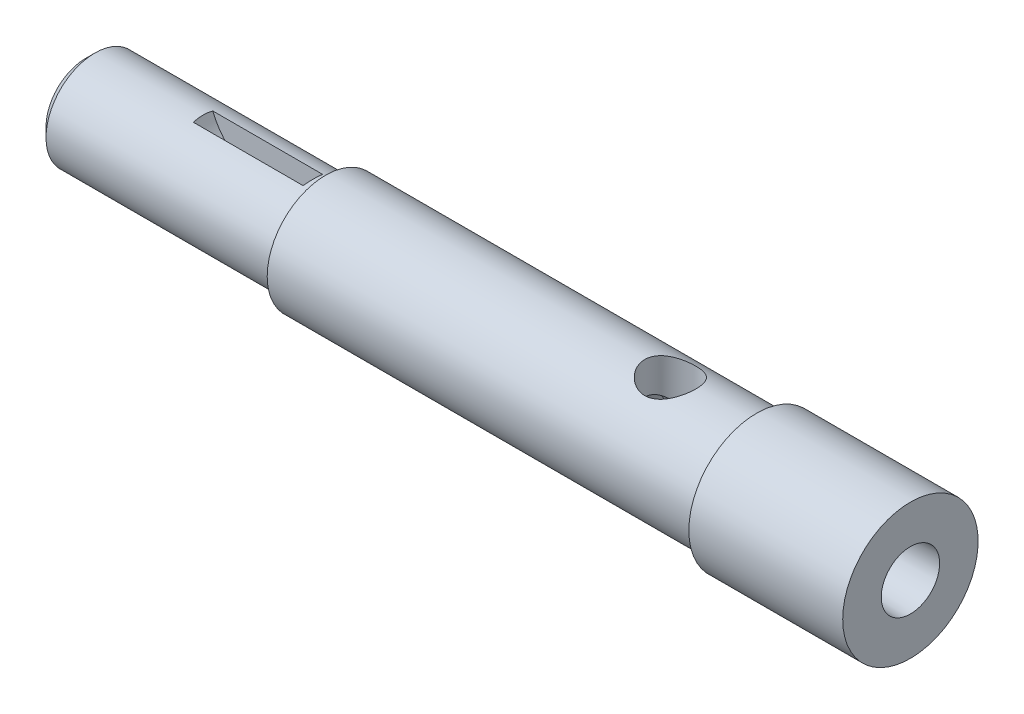
SolidWorks part; units mm, degrees
material "AISI 1020 Steel, Cold Rolled"
ref_plane "Front" through (0, 0, 0) normal (0, 0, 1) x (1, 0, 0)
ref_plane "Top" through (0, 0, 0) normal (0, 1, 0) x (1, 0, 0)
ref_plane "Right" through (0, 0, 0) normal (1, 0, 0) x (0, 0, -1)
sketch "Sketch1" plane through (0, 0, 0) normal (0, 0, 1) x (1, 0, 0)
  line L0 (-67, 0) -> (67, 0)
  line L1 (67, 0) -> (67, 11)
  line L2 (67, 11) -> (42, 11)
  line L3 (42, 11) -> (42, 9.5)
  line L4 (42, 9.5) -> (-28, 9.5)
  line L5 (-28, 9.5) -> (-28, 7.9375)
  line L6 (-28, 7.9375) -> (-67, 7.9375)
  line L7 (-67, 7.9375) -> (-67, 0)
  line L8 (-84.9355, 0) -> (103.2175, 0) construction
  dimension "D1" = 134
  dimension "D2" = 15.875
  dimension "D3" = 19
  dimension "D4" = 22
  dimension "D5" = 25
  dimension "D6" = 70
revolve "Revolve1" add sketch "Sketch1" angle 360 about L8
cosmetic thread "Cosmetic Thread1" parameters "D1"=15, "D2"=11.797
hole_wizard "1/8 NPT Tapped Hole1" positions "Sketch3" profile "Sketch2" size "1/8" standard "ANSI Inch"
sketch "Sketch3" plane through (67, 0, 0) normal (1, 0, 0) x (0, 0, -1)
  point P0 (0, 0)
sketch "Sketch2" plane through (67, 0, 0) normal (0, 1, 0) x (0, 0, -1)
  line L0 (0, 0) -> (0, 46.5335)
  line L1 (4.2164, 44) -> (0, 46.5335)
  line L2 (-4.2164, 44) -> (0, 46.5335) construction
  line L3 (4.2164, 44) -> (4.2164, 6.924)
  line L4 (4.2164, 6.924) -> (4.5374, 6.924)
  line L5 (4.5374, 6.924) -> (4.7447, 0)
  line L6 (-4.5374, 6.924) -> (-4.7447, 0) construction
  line L7 (4.7447, 0) -> (0, 0)
  line L8 (0, -6.35) -> (0, 107.95) construction
  line L11 (-4.2164, 6.924) -> (-4.5374, 6.924) construction
  dimension "Tap Drill Dia." = 8.4328
  dimension "Tap Drill Depth" = 44
  dimension "Thread Dia." = 9.4894
  dimension "Thread Angle" = 3.43
  dimension "Thread Depth" = 6.924
  dimension "Drill Angle" = 118
cosmetic thread "Hole Thread1" parameters "D1"=6.924, "D2"=10.287
sketch "Sketch4" plane through (0, 0, 0) normal (0, 1, 0) x (1, 0, 0)
  line L0 (42, 11) -> (42, -11) construction
  circle A0 centre (28, 0) radius 4.15
  dimension "D1" = 8.3
  dimension "D2" = 14
extrude "Cut-Extrude1" cut sketch "Sketch4" against normal mid plane 30
chamfer "Chamfer1" distance 1.5 angle 45 1 edges at (-67, 0, 7.9375)
ref_plane "Plane1" [suppressed] through (0, 12.6375, 0) normal (0, 1, 0) x (-1, 0, 0)
sketch "Sketch7" plane through (0, 0, 0) normal (0, 0, 1) x (1, 0, 0)
  line L0 (-28, 7.9375) -> (-65.5, 7.9375) construction
  line L1 (-55.271, 11.1125) -> (-19.7707, 11.1125) construction
  line L2 (-39, 28.0953) -> (-39, -15.815) construction
  line L3 (-28, 9.5) -> (-28, -9.5) construction
  line L4 (-48.3918, 9.525) -> (-29.6082, 9.525)
  arc A0 (-48.3918, 9.525) -> (-29.6082, 9.525) centre (-39, 11.1125) ccw
  point P5 (-39, 1.5875)
  dimension "D3" = 9.525
  dimension "D2" = 3.175
  dimension "D4" = 6.35
  dimension "D1" = 11
  dimension "D5" = 1.5875
extrude "Cut-Extrude2" cut sketch "Sketch7" against normal mid plane 3.175
